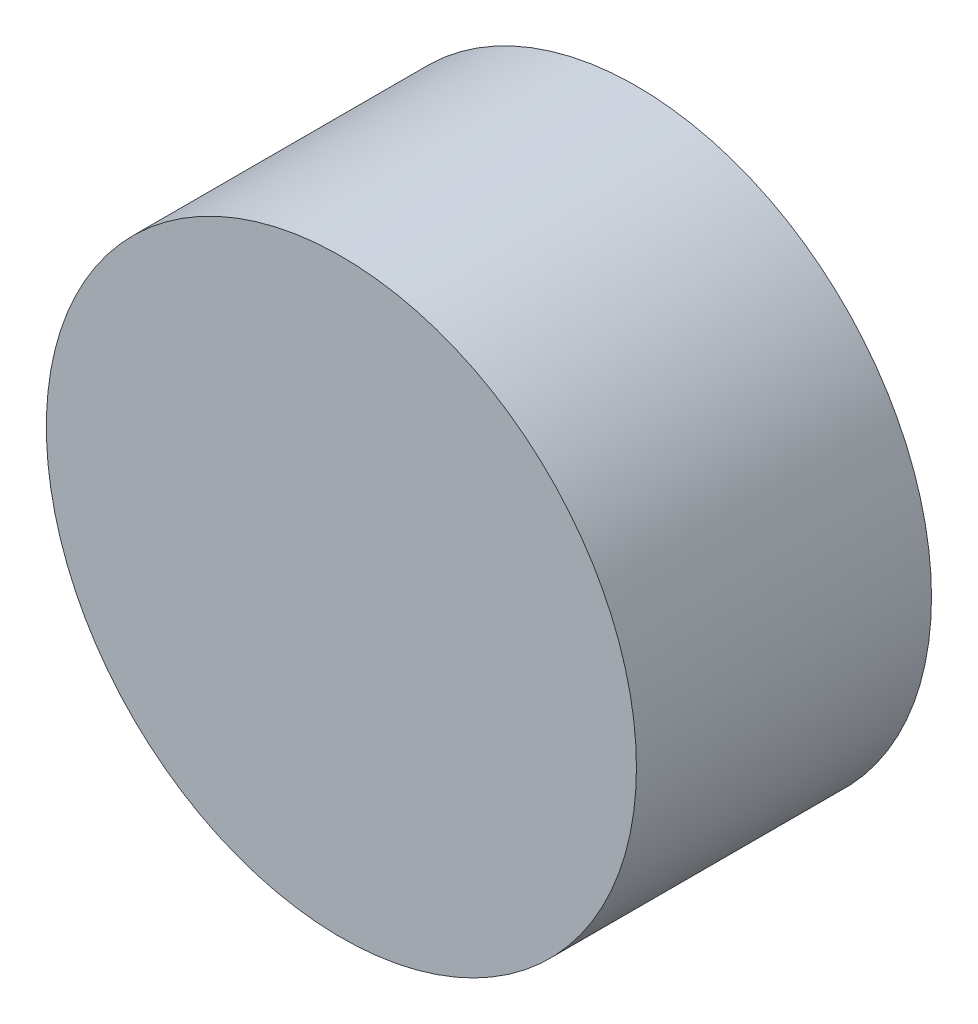
SolidWorks part; units mm, degrees
ref_plane "Front Plane" through (0, 0, 0) normal (0, 0, 1) x (1, 0, 0)
ref_plane "Top Plane" through (0, 0, 0) normal (0, 1, 0) x (1, 0, 0)
ref_plane "Right Plane" through (0, 0, 0) normal (1, 0, 0) x (0, 0, -1)
sketch "Sketch1" plane through (0, 0, 0) normal (0, 0, 1) x (1, 0, 0)
  circle A0 centre (0, 0) radius 101.6
  dimension "D1" = 203.2
extrude "Boss-Extrude1" add sketch "Sketch1" against normal blind 101.6 contours A0
